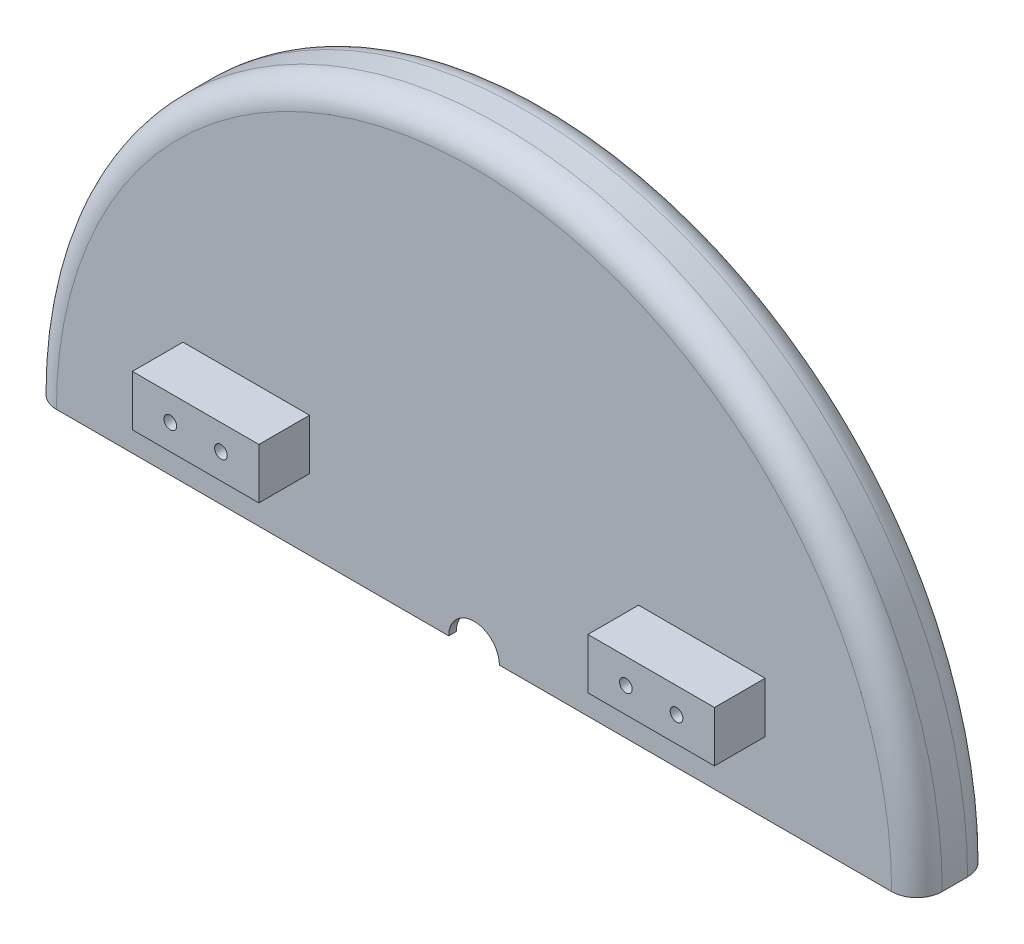
SolidWorks part; units mm, degrees
ref_plane "Front Plane" through (0, 0, 0) normal (0, 0, 1) x (1, 0, 0)
ref_plane "Top Plane" through (0, 0, 0) normal (0, 1, 0) x (1, 0, 0)
ref_plane "Right Plane" through (0, 0, 0) normal (1, 0, 0) x (0, 0, -1)
sketch "Sketch1" plane through (0, 0, 0) normal (0, 0, 1) x (1, 0, 0)
  circle A0 centre (0, 0) radius 175
  dimension "D1" = 350
extrude "Boss-Extrude3" add sketch "Sketch1" along normal blind 30
sketch "Sketch3" plane through (0, 0, 30) normal (0, 0, 1) x (1, 0, 0)
  line L0 (-175, 0) -> (175, 0)
  arc A0 (-175, 0) -> (175, 0) centre (0, 0) ccw
  circle A1 centre (0, 0) radius 175 construction
extrude "Cut-Extrude1" cut sketch "Sketch3" against normal blind 50
shell "Shell2" thickness 3
sketch "Sketch4" plane through (0, 0, 30) normal (0, 0, 1) x (1, 0, 0)
  line L0 (175, 0) -> (-175, 0) construction
  circle A0 centre (0, 0) radius 10
  dimension "D1" = 20
extrude "Cut-Extrude2" cut sketch "Sketch4" against normal blind 50
fillet "Fillet1" radius 10 2 edges at (0, 175, 0) (0, 175, 30)
sketch "Sketch6" plane through (0, 0, 0) normal (0, 0, -1) x (-1, 0, 0)
  circle A0 centre (0, 0) radius 50
  dimension "D1" = 100
extrude "Cut-Extrude4" cut sketch "Sketch6" against normal blind 10
sketch "Sketch9" plane through (0, 0, 30) normal (0, 0, 1) x (1, 0, 0)
  line L0 (-10, 0) -> (-165, 0) construction
  line L1 (-115, 48) -> (-65, 48)
  line L2 (-115, 48) -> (-115, 28)
  line L3 (-115, 28) -> (-65, 28)
  line L4 (-65, 48) -> (-65, 28)
  dimension "D1" = 20
  dimension "D2" = 50
  dimension "D3" = 55
  dimension "D4" = 48
extrude "Boss-Extrude4" add sketch "Sketch9" along normal blind 20
mirror "Mirror2" about plane through (0, 0, 0) normal (1, 0, 0) of "Boss-Extrude4"
hole_wizard "Ø5.0 (5) Diameter Hole2" positions "Sketch12" profile "Sketch11" hole size "Ø5.0" standard "ISO"
sketch "Sketch12" plane through (0, 0, 50) normal (0, 0, 1) x (1, 0, 0)
  line L0 (-10, 0) -> (-165, 0) construction
  line L1 (165, 0) -> (10, 0) construction
  point P0 (-100, 38)
  point P1 (-80, 38)
  point P3 (80, 38)
  point P5 (100, 38)
  dimension "D1" = 20
  dimension "D2" = 20
  dimension "D3" = 70
  dimension "D4" = 70
  dimension "D5" = 38
  dimension "D6" = 38
sketch "Sketch11" plane through (-100, 38, 50) normal (1, 0, 0) x (0, -1, 0)
  line L0 (0, 0) -> (0, 12.5022)
  line L1 (0, 12.5022) -> (2.5, 11)
  line L2 (2.5, 11) -> (2.5, 0)
  line L5 (2.5, 0) -> (0, 0)
  line L10 (0, 12.5022) -> (-2.5, 11) construction
  line L11 (0, -6.35) -> (0, 107.95) construction
  dimension "Hole Dia." = 5
  dimension "Hole Depth" = 11
  dimension "Drill Angle" = 118
cosmetic thread "Cosmetic Thread1" parameters "D2"=6
cosmetic thread "Cosmetic Thread2" parameters "D2"=6
cosmetic thread "Cosmetic Thread3" parameters "D2"=6
cosmetic thread "Cosmetic Thread4" parameters "D2"=6
